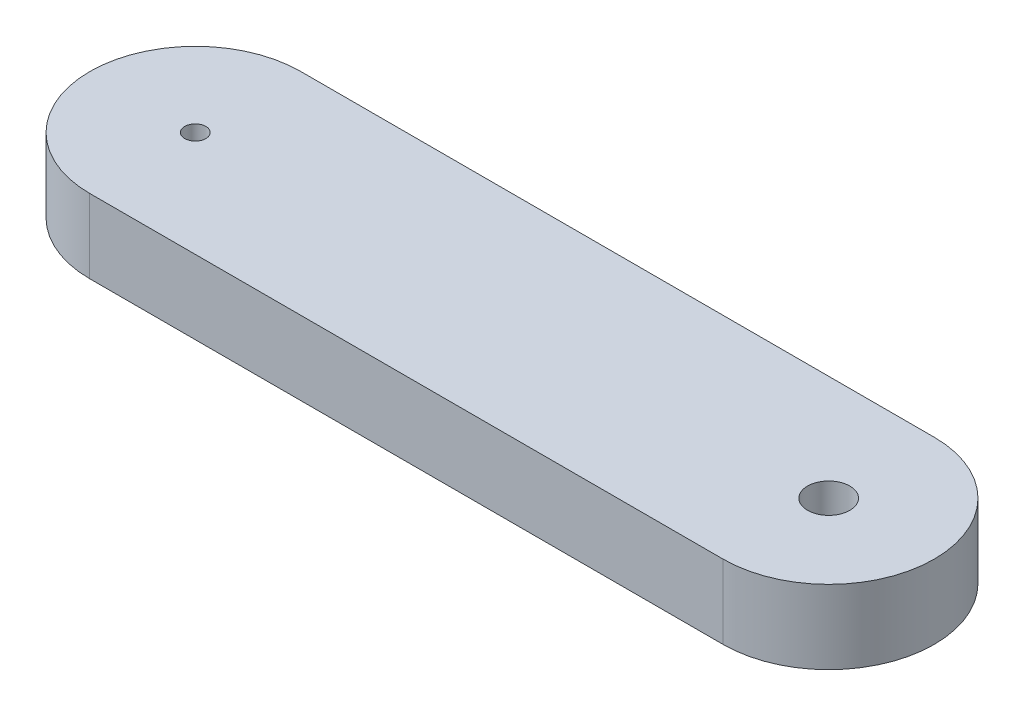
SolidWorks part; units mm, degrees
ref_plane "Front Plane" through (0, 0, 0) normal (0, 0, 1) x (1, 0, 0)
ref_plane "Top Plane" through (0, 0, 0) normal (0, 1, 0) x (1, 0, 0)
ref_plane "Right Plane" through (0, 0, 0) normal (1, 0, 0) x (0, 0, -1)
sketch "Sketch1" plane through (0, 0, 0) normal (0, 1, 0) x (1, 0, 0)
  line L0 (0, 0) -> (600, 0) construction
  line L1 (0, 100) -> (600, 100)
  line L2 (0, -100) -> (600, -100)
  arc A0 (0, 100) -> (0, -100) centre (0, 0) ccw
  arc A1 (600, -100) -> (600, 100) centre (600, 0) ccw
  point P3 (300, 0)
  dimension "D1" = 600
extrude "Boss-Extrude1" add sketch "Sketch1" along normal blind 70 contours L2 A1 L1 A0
sketch "Sketch2" plane through (0, 70, 0) normal (0, 1, 0) x (1, 0, 0)
  circle A0 centre (0, 0) radius 10
extrude "Cut-Extrude1" cut sketch "Sketch2" against normal blind 20
sketch "Sketch3" plane through (0, 70, 0) normal (0, 1, 0) x (1, 0, 0)
  circle A0 centre (600, 0) radius 20
extrude "Cut-Extrude2" cut sketch "Sketch3" against normal through all
